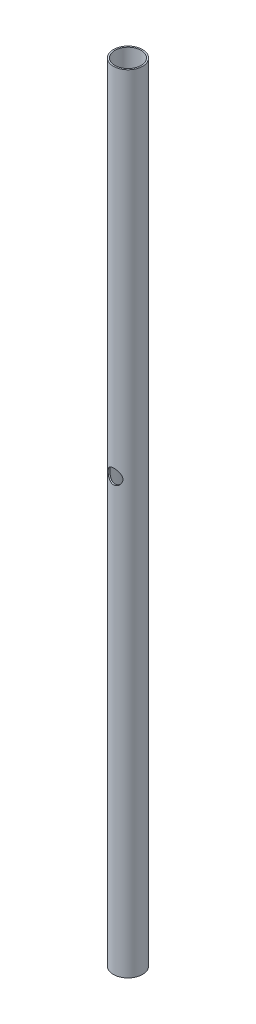
SolidWorks part; units mm, degrees
material "AISI 316 Stainless Steel Sheet (SS)"
ref_plane "Front Plane" through (0, 0, 0) normal (0, 0, 1) x (1, 0, 0)
ref_plane "Top Plane" through (0, 0, 0) normal (0, 1, 0) x (1, 0, 0)
ref_plane "Right Plane" through (0, 0, 0) normal (1, 0, 0) x (0, 0, -1)
sketch "Sketch1" plane through (0, 0, 0) normal (0, 1, 0) x (1, 0, 0)
  circle A0 centre (0, 0) radius 0.5
  circle A1 centre (0, 0) radius 0.45
  dimension "D1" = 0.05
  dimension "D2" = 1
extrude "Boss-Extrude1" add sketch "Sketch1" along normal blind 27
hole_wizard "Ø0.5 (0.5) Diameter Hole1" positions "3DSketch1" profile "Sketch2" hole size "Ø0.5" standard "ISO" end condition through all
sketch3d "3DSketch1"
  point P0 (-0.0061, 14.81, -0.5)
sketch "Sketch2" plane through (-0.0061, 14.81, -0.5) normal (0, 1, 0) x (-0.9999, 0, 0.0122)
  line L0 (0, 0) -> (0, 1.006)
  line L1 (0, 1.006) -> (0.25, 1.006)
  line L2 (0.25, 1.006) -> (0.25, 0)
  line L5 (0.25, 0) -> (0, 0)
  line L11 (0, -6.35) -> (0, 107.95) construction
  dimension "Thru Hole Dia." = 0.5
  dimension "Thru Hole Depth" = 1.006
